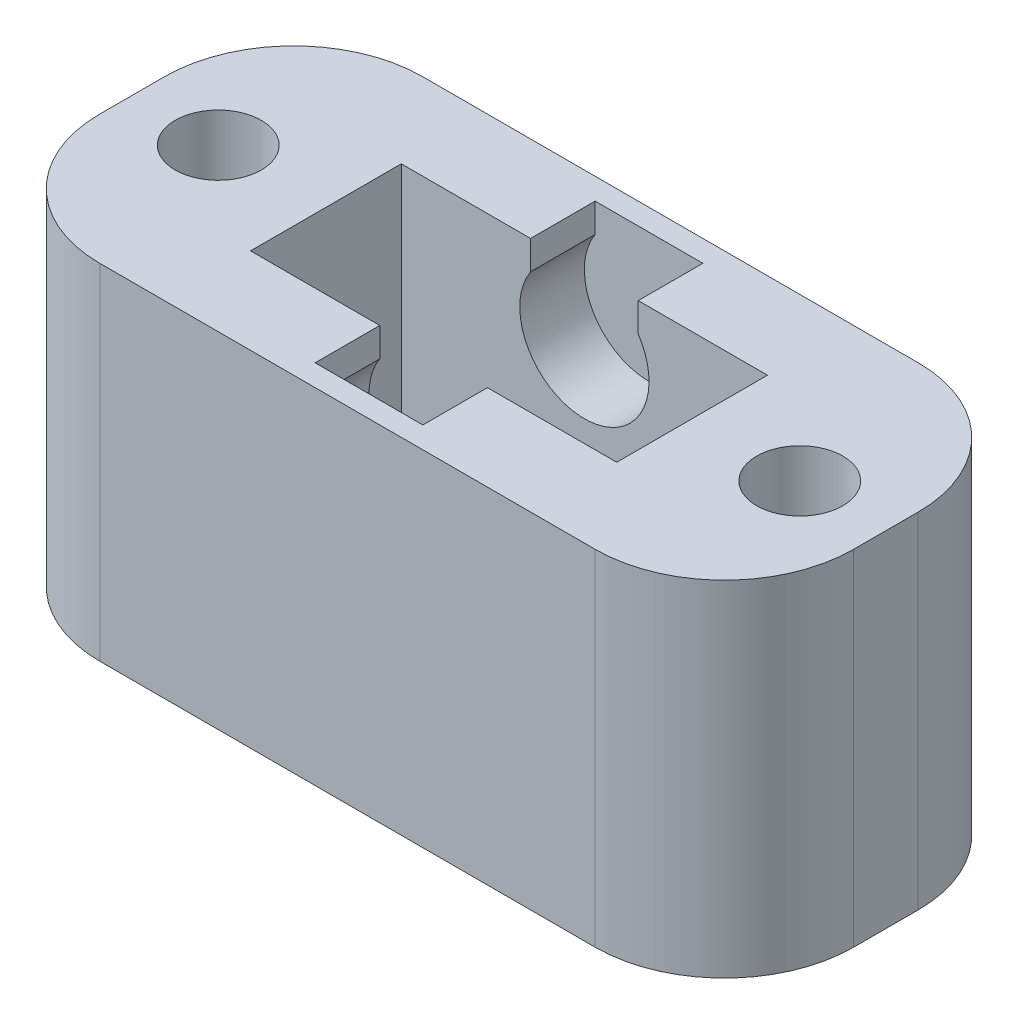
SolidWorks part; units mm, degrees
ref_plane "Front Plane" through (0, 0, 0) normal (0, 0, 1) x (1, 0, 0)
ref_plane "Top Plane" through (0, 0, 0) normal (0, 1, 0) x (1, 0, 0)
ref_plane "Right Plane" through (0, 0, 0) normal (1, 0, 0) x (0, 0, -1)
sketch "Sketch1" plane through (0, 0, 0) normal (0, 1, 0) x (1, 0, 0)
  line L0 (-5.75, 3.75) -> (-5.75, -3.75) construction
  line L1 (-4.25, -1.75) -> (4.25, -1.75)
  line L2 (-4.25, -1.75) -> (-4.25, 1.75)
  line L3 (-4.25, 1.75) -> (4.25, 1.75)
  line L4 (4.25, -1.75) -> (4.25, 1.75)
  line L5 (-4.25, -1.75) -> (4.25, 1.75) construction
  line L6 (-4.25, 1.75) -> (4.25, -1.75) construction
  line L7 (-8.75, -3.75) -> (8.75, -3.75)
  line L8 (-8.75, -3.75) -> (-8.75, 3.75)
  line L9 (-8.75, 3.75) -> (8.75, 3.75)
  line L10 (8.75, -3.75) -> (8.75, 3.75)
  line L11 (-8.75, -3.75) -> (8.75, 3.75) construction
  line L12 (-8.75, 3.75) -> (8.75, -3.75) construction
  line L13 (8.75, 0) -> (-8.75, 0) construction
  line L14 (-7.75, 3.75) -> (-7.75, -3.75) construction
  line L15 (0, 3.75) -> (0, -3.75) construction
  circle A0 centre (-6.75, 0) radius 1
  circle A1 centre (6.75, 0) radius 1
  point P0 (0, 0)
  point P6 (0, 0)
  dimension "D3" = 2
  dimension "D1" = 8.5
  dimension "D2" = 3.5
  dimension "D4" = 1.5
  dimension "D5" = 1
  dimension "D6" = 2
extrude "Boss-Extrude1" add sketch "Sketch1" along normal blind 8
sketch "Sketch2" plane through (0, 0, 0) normal (0, -1, 0) x (1, 0, 0)
  line L1 (-8.75, 3.75) -> (8.75, 3.75)
  line L2 (-8.75, 3.75) -> (-8.75, -3.75)
  line L3 (-8.75, -3.75) -> (8.75, -3.75)
  line L4 (8.75, 3.75) -> (8.75, -3.75)
extrude "Boss-Extrude2" [suppressed] add sketch "Sketch2" along normal blind 1
fillet "Fillet1" radius 3 4 edges at (-8.75, 4, 3.75) (-8.75, 4, -3.75) (8.75, 4, -3.75) (8.75, 4, 3.75)
sketch "Sketch3" plane through (0, 0, 1.75) normal (0, 0, -1) x (-1, 0, 0)
  line L0 (0, 8) -> (0, 0) construction
  line L1 (4.25, 8) -> (-4.25, 8) construction
  line L2 (-4.5, 6.5) -> (4.5, 6.5) construction
  line L6 (-1.25, 6.5) -> (1.25, 6.5)
  line L7 (-1.25, 6.5) -> (-1.25, 8)
  line L8 (-1.25, 8) -> (1.25, 8)
  line L9 (1.25, 6.5) -> (1.25, 8)
  line L10 (-1.25, 6.5) -> (1.25, 8) construction
  line L11 (-1.25, 8) -> (1.25, 6.5) construction
  circle A0 centre (0, 6.5) radius 1.5
  point P7 (0, 4)
  point P13 (0, 7.25)
  line M4 (4.25, 8) -> (-4.25, 8)
  dimension "D1" = 3
  dimension "D2" = 2.5
  dimension "D3" = 2.5
extrude "Cut-Extrude1" cut sketch "Sketch3" against normal blind 1.5 contours L7 A0 L9 L6 | L9 A0 L7 L6 | A0 L9 L7 M4 | A0 L8 L7
chamfer "Chamfer1" [suppressed] distance 0.5 angle 81
mirror "Mirror1" about plane through (0, 0, 0) normal (0, 0, 1) of "Cut-Extrude1"
